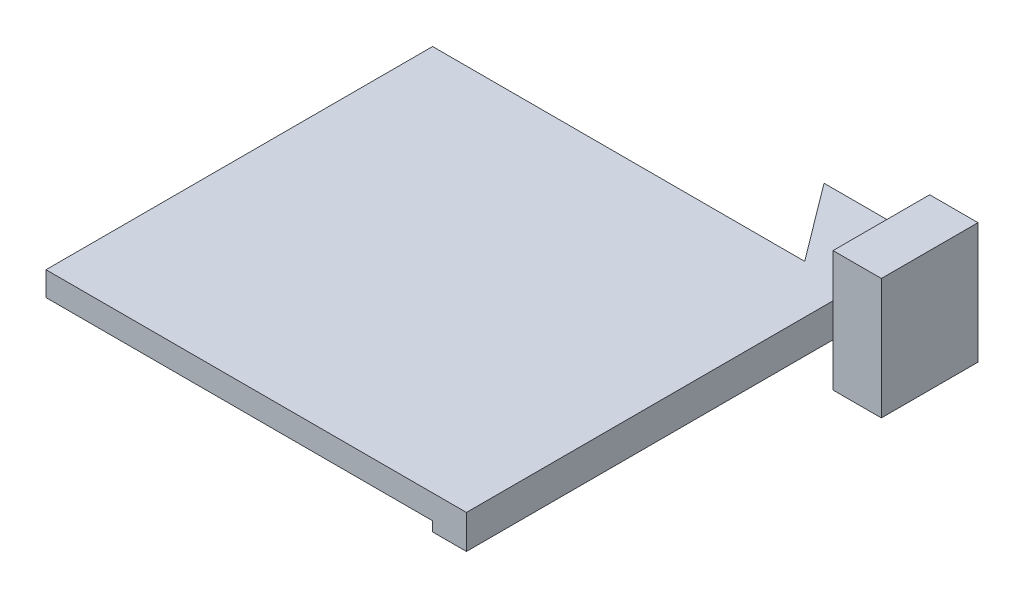
SolidWorks part; units mm, degrees
ref_plane "Front Plane" through (0, 0, 0) normal (0, 0, 1) x (1, 0, 0)
ref_plane "Top Plane" through (0, 0, 0) normal (0, 1, 0) x (1, 0, 0)
ref_plane "Right Plane" through (0, 0, 0) normal (1, 0, 0) x (0, 0, -1)
sketch "Sketch1" plane through (0, 0, 0) normal (0, 0, 1) x (1, 0, 0)
  line L1 (-3.5, -3.5) -> (3.5, -3.5)
  line L2 (-3.5, -3.5) -> (-3.5, 3.5)
  line L3 (-3.5, 3.5) -> (3.5, 3.5)
  line L4 (3.5, -3.5) -> (3.5, 3.5)
  line L5 (-3.5, -3.5) -> (3.5, 3.5) construction
  line L6 (-3.5, 3.5) -> (3.5, -3.5) construction
  point P0 (0, 0)
  dimension "D1" = 7
  dimension "D2" = 7
extrude "Boss-Extrude1" add sketch "Sketch1" along normal blind 100
sketch "Sketch3" plane through (0, 3.5, 0) normal (0, 1, 0) x (1, 0, 0)
  line L1 (-3.5, -100) -> (-83.5, -100)
  line L2 (-3.5, -100) -> (-3.5, -20)
  line L3 (-3.5, -20) -> (-83.5, -20)
  line L4 (-83.5, -100) -> (-83.5, -20)
extrude "Boss-Extrude2" add sketch "Sketch3" against normal blind 5
sketch "Sketch8" plane through (0, -3.5, 0) normal (0, -1, 0) x (1, 0, 0)
  line L0 (-3.5, 20) -> (-6.5, 20)
  line L1 (-3.5, 100) -> (-3.5, 0) construction
  line L2 (-3.5, 4) -> (-3.5, 20)
  line L3 (-3.5, 4) -> (-18.5, 4)
  line L4 (-18.5, 4) -> (-6.5, 20)
extrude "Boss-Extrude5" add sketch "Sketch8" against normal blind 7
sketch "Sketch11" plane through (3.5, 0, 0) normal (1, 0, 0) x (0, 0, -1)
  line L8 (-4.1373, -12.5) -> (-24.1373, -12.5)
  line L9 (-4.1373, -12.5) -> (-4.1373, 12.5)
  line L10 (-4.1373, 12.5) -> (-24.1373, 12.5)
  line L11 (-24.1373, -12.5) -> (-24.1373, 12.5)
  line L12 (-4.1373, -12.5) -> (-24.1373, 12.5) construction
  line L13 (-4.1373, 12.5) -> (-24.1373, -12.5) construction
  point P5 (-14.1373, 0)
extrude "Boss-Extrude6" add sketch "Sketch11" along normal blind 10
